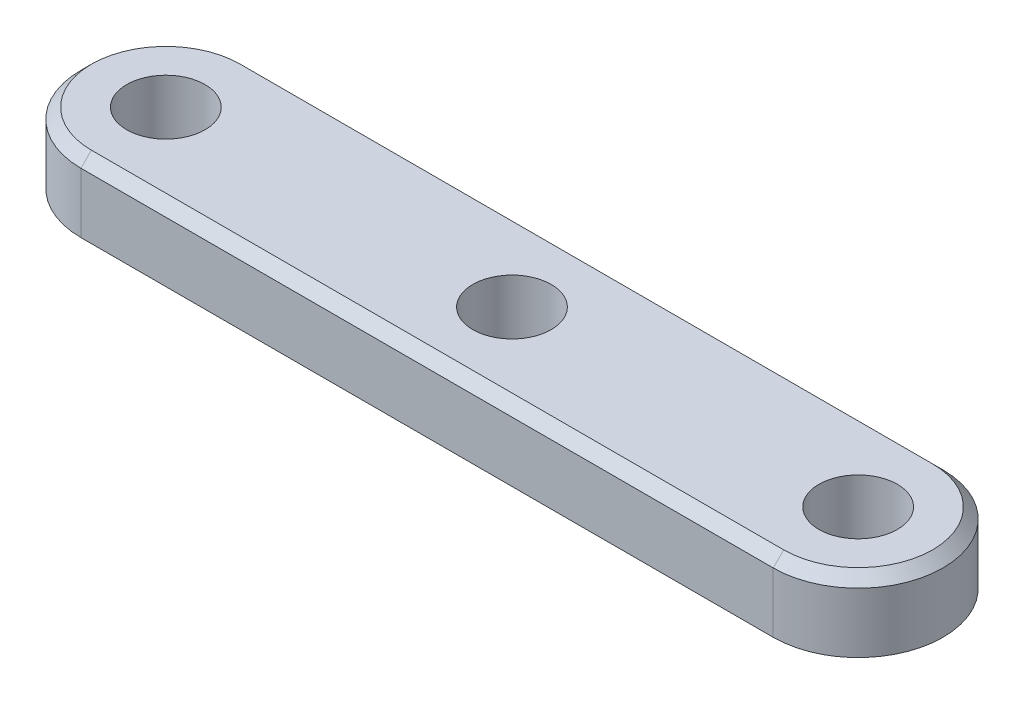
SolidWorks part; units mm, degrees
ref_plane "Front Plane" through (0, 0, 0) normal (0, 0, 1) x (1, 0, 0)
ref_plane "Top Plane" through (0, 0, 0) normal (0, 1, 0) x (1, 0, 0)
ref_plane "Right Plane" through (0, 0, 0) normal (1, 0, 0) x (0, 0, -1)
sketch "Sketch1" plane through (0, 0, 0) normal (0, 1, 0) x (1, 0, 0)
  line L0 (-18.0944, 0) -> (24.4801, 0) construction
  line L1 (-13.25, 0) -> (13.25, 0) construction
  line L2 (-13.25, 3.25) -> (13.25, 3.25)
  line L3 (-13.25, -3.25) -> (13.25, -3.25)
  line L4 (0, 10.1131) -> (0, -14.786) construction
  arc A0 (-13.25, 3.25) -> (-13.25, -3.25) centre (-13.25, 0) ccw
  arc A1 (13.25, -3.25) -> (13.25, 3.25) centre (13.25, 0) ccw
  circle A2 centre (-13.25, 0) radius 1.5
  circle A4 centre (13.25, 0) radius 1.5
  circle A5 centre (0, 0) radius 1.5
  point P5 (0, 0)
  point P11 (-16.5, 0)
  point P12 (16.5, 0)
  dimension "D3" = 3
  dimension "D4" = 3
  dimension "D1" = 6.5
  dimension "D2" = 33
extrude "Boss-Extrude1" add sketch "Sketch1" along normal mid plane 2.7
chamfer "Chamfer1" distance 0.4 angle 45 4 edges at (16.5, 1.35, 0) (0, 1.35, -3.25) (-16.5, 1.35, 0) (0, 1.35, 3.25)
